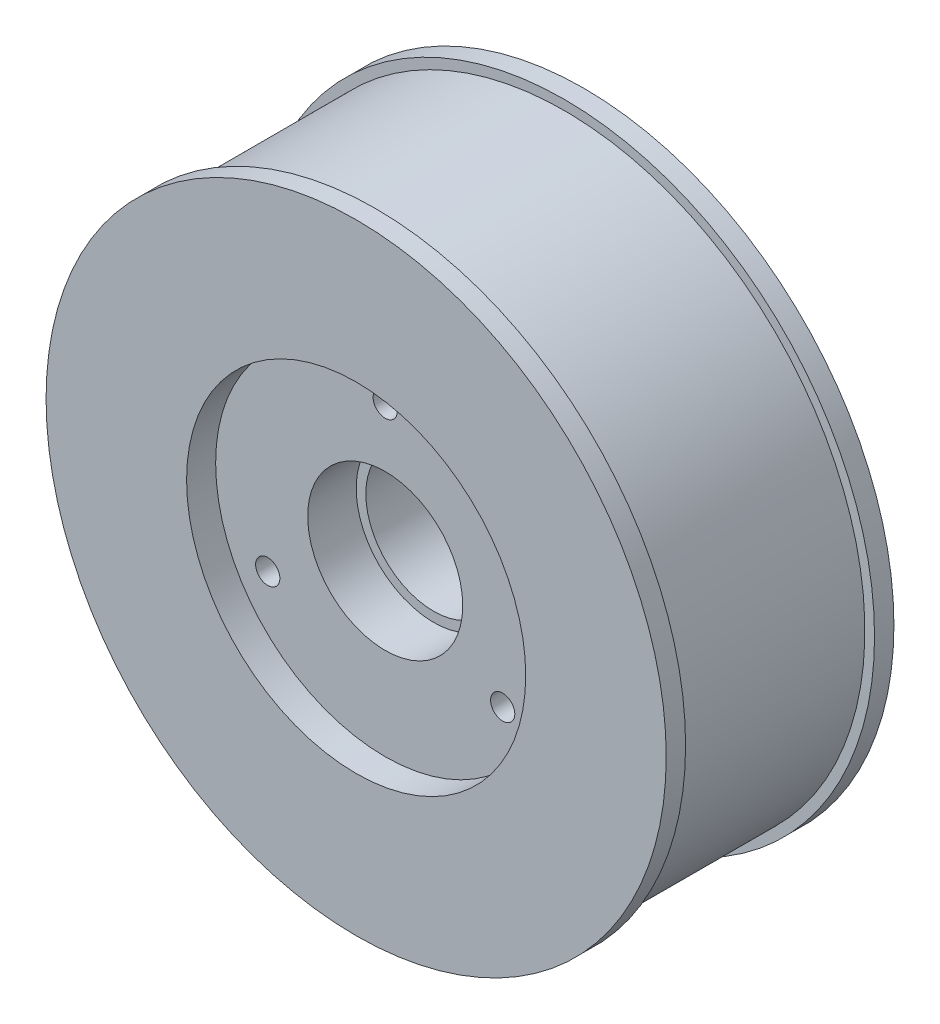
SolidWorks part; units mm, degrees
ref_plane "Front Plane" through (0, 0, 0) normal (0, 0, 1) x (1, 0, 0)
ref_plane "Top Plane" through (0, 0, 0) normal (0, 1, 0) x (1, 0, 0)
ref_plane "Right Plane" through (0, 0, 0) normal (1, 0, 0) x (0, 0, -1)
sketch "Sketch1" plane through (0, 0, 0) normal (0, 0, 1) x (1, 0, 0)
  circle A0 centre (0, 0) radius 31
  dimension "D1" = 62
extrude "Extrude1" add sketch "Sketch1" along normal blind 19.5
sketch "Sketch2" plane through (0, 0, 19.5) normal (0, 0, 1) x (1, 0, 0)
  circle A0 centre (0, 0) radius 32
  dimension "D1" = 64
extrude "Extrude2" add sketch "Sketch2" along normal blind 2
sketch "Sketch3" plane through (0, 0, 0) normal (0, 0, -1) x (-1, 0, 0)
  circle A0 centre (0, 0) radius 32
  dimension "D1" = 64
extrude "Extrude3" add sketch "Sketch3" along normal blind 2
sketch "Sketch4" plane through (0, 0, -2) normal (0, 0, -1) x (-1, 0, 0)
  circle A0 centre (0, 0) radius 7
  dimension "D1" = 14
extrude "Cut-Extrude1" cut sketch "Sketch4" against normal through all
sketch "Sketch5" plane through (0, 0, -2) normal (0, 0, -1) x (-1, 0, 0)
  circle A0 centre (0, 0) radius 8
  dimension "D1" = 16
extrude "Cut-Extrude2" cut sketch "Sketch5" against normal blind 9.5
sketch "Sketch6" plane through (0, 0, -2) normal (0, 0, -1) x (-1, 0, 0)
  circle A0 centre (0, 0) radius 18
  dimension "D1" = 36
extrude "Cut-Extrude3" cut sketch "Sketch6" against normal blind 5
ref_point "Point1"
hole_wizard "M3x0.5 Tapped Hole1" positions "3DSketch1" profile "Sketch7" tap size "M3x0.5" standard "Ansi Metric" end condition through all
sketch3d "3DSketch1"
  line L0 (0, 0, 3) -> (0, 14, 3) construction
  line L1 (0, 0, 7.5) -> (0, 0, 3) construction
  line L3 (12.1244, -7, 3) -> (0, 0, 3) construction
  line L4 (0, 0, 3) -> (-12.1244, -7, 3) construction
  point P0 (0, 14, 3)
  point P2 (12.1244, -7, 3)
  point P4 (-12.1244, -7, 3)
  dimension "D1" = 14
  dimension "D2" = 14
  dimension "D3" = 14
  dimension "D4" = 120
  dimension "D5" = 120
cosmetic thread "Hole Thread1" parameters "D2"=3
cosmetic thread "Hole Thread2" parameters "D2"=3
cosmetic thread "Hole Thread3" parameters "D2"=3
sketch "Sketch7" plane through (0, 14, 3) normal (1, 0, 0) x (0, 1, 0)
  line L0 (0, 0) -> (0, 18.5)
  line L1 (0, 18.5) -> (1.25, 18.5)
  line L2 (1.25, 18.5) -> (1.25, 0)
  line L5 (1.25, 0) -> (0, 0)
  line L11 (0, -6.35) -> (0, 107.95) construction
  dimension "Thru Tap Drill Dia." = 2.5
  dimension "Thru Tap Drill Depth" = 18.5
sketch "Sketch8" plane through (0, 0, 21.5) normal (0, 0, 1) x (1, 0, 0)
  circle A0 centre (0, 0) radius 8
  dimension "D1" = 16
extrude "Cut-Extrude4" cut sketch "Sketch8" against normal blind 8
sketch "Sketch9" plane through (0, 0, 21.5) normal (0, 0, 1) x (1, 0, 0)
  circle A0 centre (0, 0) radius 17.5
  dimension "D1" = 35
extrude "Cut-Extrude5" cut sketch "Sketch9" against normal blind 3
